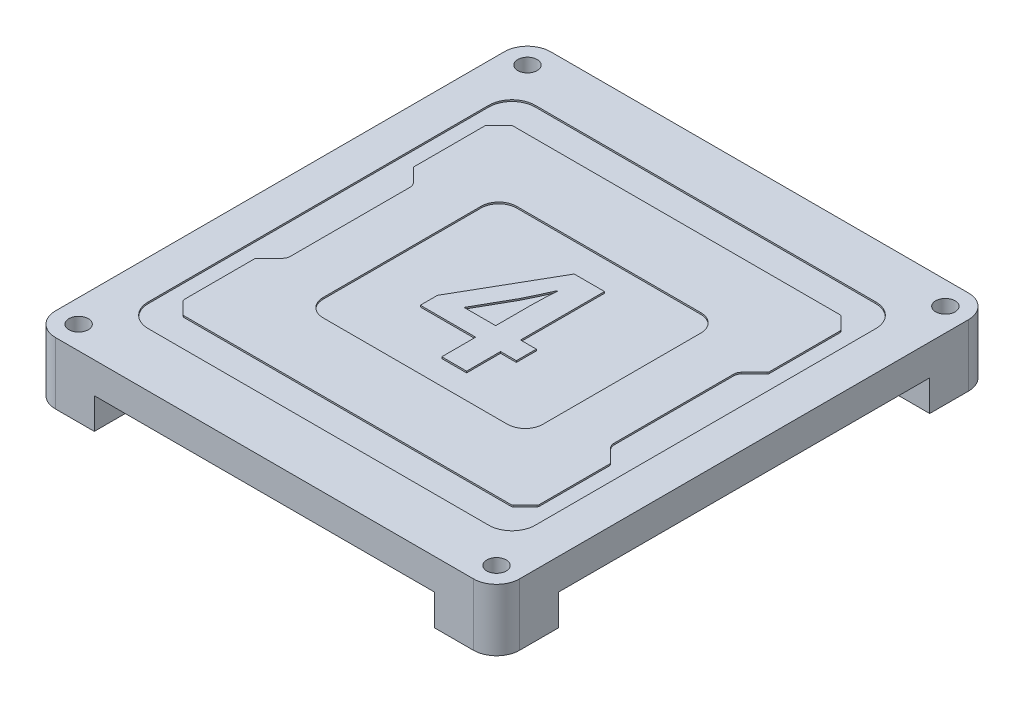
SolidWorks part; units mm, degrees
ref_plane "前视基准面" through (0, 0, 0) normal (0, 0, 1) x (1, 0, 0)
ref_plane "上视基准面" through (0, 0, 0) normal (0, 1, 0) x (1, 0, 0)
ref_plane "右视基准面" through (0, 0, 0) normal (1, 0, 0) x (0, 0, -1)
other "Configuration Table"
sketch "草图1" plane through (0, 0, 0) normal (0, 1, 0) x (1, 0, 0)
  line L8 (-27.0001, -31.9874) -> (27.0001, -31.9874)
  line L9 (29.9874, -29.0001) -> (29.9874, 29.0001)
  line L10 (27.0001, 31.9874) -> (-27.0001, 31.9874)
  line L11 (-29.9874, 29.0001) -> (-29.9874, -29.0001)
  line L12 (-27.0001, -31.9874) -> (27.0001, -31.9874)
  line L13 (29.9874, -29.0001) -> (29.9874, 29.0001)
  line L14 (27.0001, 31.9874) -> (-27.0001, 31.9874)
  line L15 (-29.9874, 29.0001) -> (-29.9874, -29.0001)
  arc A4 (27.0001, -31.9874) -> (29.9874, -29.0001) centre (27.0001, -29.0001) ccw
  arc A5 (29.9874, 29.0001) -> (27.0001, 31.9874) centre (27.0001, 29.0001) ccw
  arc A6 (-27.0001, 31.9874) -> (-29.9874, 29.0001) centre (-27.0001, 29.0001) ccw
  arc A7 (-29.9874, -29.0001) -> (-27.0001, -31.9874) centre (-27.0001, -29.0001) ccw
  arc A8 (27.0001, -31.9874) -> (29.9874, -29.0001) centre (27.0001, -29.0001) ccw
  arc A9 (29.9874, 29.0001) -> (27.0001, 31.9874) centre (27.0001, 29.0001) ccw
  arc A10 (-27.0001, 31.9874) -> (-29.9874, 29.0001) centre (-27.0001, 29.0001) ccw
  arc A11 (-29.9874, -29.0001) -> (-27.0001, -31.9874) centre (-27.0001, -29.0001) ccw
  dimension "D1" = 0
extrude "凸台-拉伸1" add sketch "草图1" along normal blind 4
sketch "草图2" plane through (0, 0, 0) normal (0, -1, 0) x (1, 0, 0)
  line L4 (-21.9874, 23.9874) -> (-21.9874, 31.9874)
  line L5 (-21.9874, 31.9874) -> (-27.0001, 31.9874)
  line L6 (-29.9874, 29.0001) -> (-29.9874, 23.9874)
  line L7 (-29.9874, 23.9874) -> (-21.9874, 23.9874)
  line L8 (-21.9874, 23.9874) -> (-21.9874, 31.9874)
  line L9 (-21.9874, 31.9874) -> (-27.0001, 31.9874)
  line L10 (-29.9874, 29.0001) -> (-29.9874, 23.9874)
  line L11 (-29.9874, 23.9874) -> (-21.9874, 23.9874)
  line L12 (21.9874, -23.9874) -> (21.9874, -31.9874)
  line L13 (21.9874, -31.9874) -> (27.0001, -31.9874)
  line L14 (29.9874, -29.0001) -> (29.9874, -23.9874)
  line L15 (29.9874, -23.9874) -> (21.9874, -23.9874)
  line L16 (21.9874, -23.9874) -> (21.9874, -31.9874)
  line L17 (21.9874, -31.9874) -> (27.0001, -31.9874)
  line L18 (29.9874, -29.0001) -> (29.9874, -23.9874)
  line L19 (29.9874, -23.9874) -> (21.9874, -23.9874)
  line L20 (21.9874, 23.9874) -> (29.9874, 23.9874)
  line L21 (29.9874, 23.9874) -> (29.9874, 29.0001)
  line L22 (27.0001, 31.9874) -> (21.9874, 31.9874)
  line L23 (21.9874, 31.9874) -> (21.9874, 23.9874)
  line L24 (21.9874, 23.9874) -> (29.9874, 23.9874)
  line L25 (29.9874, 23.9874) -> (29.9874, 29.0001)
  line L26 (27.0001, 31.9874) -> (21.9874, 31.9874)
  line L27 (21.9874, 31.9874) -> (21.9874, 23.9874)
  line L28 (-29.9874, -23.9874) -> (-29.9874, -29.0001)
  line L29 (-21.9874, -23.9874) -> (-29.9874, -23.9874)
  line L30 (-21.9874, -31.9874) -> (-21.9874, -23.9874)
  line L31 (-27.0001, -31.9874) -> (-21.9874, -31.9874)
  line L32 (-29.9874, -23.9874) -> (-29.9874, -29.0001)
  line L33 (-21.9874, -23.9874) -> (-29.9874, -23.9874)
  line L34 (-21.9874, -31.9874) -> (-21.9874, -23.9874)
  line L35 (-27.0001, -31.9874) -> (-21.9874, -31.9874)
  arc A1 (-27.0001, 31.9874) -> (-29.9874, 29.0001) centre (-27.0001, 29.0001) ccw
  arc A2 (-27.0001, 31.9874) -> (-29.9874, 29.0001) centre (-27.0001, 29.0001) ccw
  arc A3 (27.0001, -31.9874) -> (29.9874, -29.0001) centre (27.0001, -29.0001) ccw
  arc A4 (27.0001, -31.9874) -> (29.9874, -29.0001) centre (27.0001, -29.0001) ccw
  arc A5 (29.9874, 29.0001) -> (27.0001, 31.9874) centre (27.0001, 29.0001) ccw
  arc A6 (29.9874, 29.0001) -> (27.0001, 31.9874) centre (27.0001, 29.0001) ccw
  arc A7 (-29.9874, -29.0001) -> (-27.0001, -31.9874) centre (-27.0001, -29.0001) ccw
  arc A8 (-29.9874, -29.0001) -> (-27.0001, -31.9874) centre (-27.0001, -29.0001) ccw
  dimension "D1" = 0
  dimension "D2" = 0
  dimension "D3" = 0
  dimension "D4" = 0
extrude "凸台-拉伸2" add sketch "草图2" along normal blind 4
sketch "草图3" plane through (0, -4, 0) normal (0, -1, 0) x (1, 0, 0)
  circle A0 centre (-27.0001, 29.0001) radius 1.25
  circle A1 centre (27.0001, 29.0001) radius 1.25
  circle A2 centre (27.0001, -29.0001) radius 1.25
  circle A3 centre (-27.0001, -29.0001) radius 1.25
  dimension "D1" = 2.5
  dimension "D2" = 2.5
  dimension "D3" = 2.5
  dimension "D4" = 2.5
extrude "切除-拉伸1" cut sketch "草图3" against normal blind 15
sketch "草图4" plane through (0, 4, 0) normal (0, 1, 0) x (1, 0, 0)
  line L1 (-22, -25) -> (22, -25)
  line L2 (-25, -22) -> (-25, 22)
  line L3 (-22, 25) -> (22, 25)
  line L4 (25, -22) -> (25, 22)
  line L5 (0, 25) -> (0, -25) construction
  line L6 (-25, 0) -> (25, 0) construction
  arc A0 (-22, -25) -> (-25, -22) centre (-22, -22) cw
  arc A1 (25, 22) -> (22, 25) centre (22, 22) ccw
  arc A2 (25, -22) -> (22, -25) centre (22, -22) cw
  arc A3 (-25, 22) -> (-22, 25) centre (-22, 22) cw
  point P0 (0, 0)
  point P6 (-25, -25)
  point P16 (-25, 25)
  dimension "D2" = 3
  dimension "D1" = 50
extrude "切除-拉伸2" cut sketch "草图4" against normal blind 0.2
sketch "草图9" plane through (0, 3.8, 0) normal (0, 1, 0) x (1, 0, 0)
  line L4 (-20.91, 7.7375) -> (-20.91, -7.7375)
  line L5 (-21.2088, -8.4588) -> (-22.8504, -10.1004)
  line L6 (-22.95, -10.3408) -> (-22.95, -19.4092)
  line L7 (-22.8504, -19.6496) -> (-21.3496, -21.1504)
  line L8 (-21.1092, -21.25) -> (21.1092, -21.25)
  line L9 (21.3496, -21.1504) -> (22.8504, -19.6496)
  line L10 (22.95, -19.4092) -> (22.95, -10.3408)
  line L11 (22.8504, -10.1004) -> (21.2088, -8.4588)
  line L12 (20.91, -7.7375) -> (20.91, 7.7375)
  line L13 (21.2088, 8.4588) -> (22.8504, 10.1004)
  line L14 (22.95, 10.3408) -> (22.95, 19.4092)
  line L15 (22.8504, 19.6496) -> (21.3496, 21.1504)
  line L16 (21.1092, 21.25) -> (-21.1092, 21.25)
  line L17 (-21.3496, 21.1504) -> (-22.8504, 19.6496)
  line L18 (-22.95, 19.4092) -> (-22.95, 10.3408)
  line L19 (-22.8504, 10.1004) -> (-21.2088, 8.4588)
  line L20 (-11.9, -12.495) -> (11.9, -12.495)
  line L21 (14.195, -10.2) -> (14.195, 10.2)
  line L22 (-14.195, 10.2) -> (-14.195, -10.2)
  line L23 (11.9, 12.495) -> (-11.9, 12.495)
  line L24 (-11.9, 0) -> (11.9, 0) construction
  line L25 (0, 11.305) -> (0, -11.305) construction
  line L27 (-10.9, -10.2) -> (10.9, -10.2)
  line L28 (-11.9, -9.2) -> (-11.9, 9.2)
  line L29 (-10.9, 10.2) -> (10.9, 10.2)
  line L30 (11.9, -9.2) -> (11.9, 9.2)
  line L31 (0, 10.2) -> (0, -10.2) construction
  line L32 (-11.9, 0) -> (11.9, 0) construction
  arc A4 (-20.91, 7.7375) -> (-21.2088, 8.4588) centre (-21.93, 7.7375) ccw
  arc A5 (-21.2088, -8.4588) -> (-20.91, -7.7375) centre (-21.93, -7.7375) ccw
  arc A6 (-22.8504, -10.1004) -> (-22.95, -10.3408) centre (-22.61, -10.3408) ccw
  arc A7 (-22.95, -19.4092) -> (-22.8504, -19.6496) centre (-22.61, -19.4092) ccw
  arc A8 (-21.3496, -21.1504) -> (-21.1092, -21.25) centre (-21.1092, -20.91) ccw
  arc A9 (21.1092, -21.25) -> (21.3496, -21.1504) centre (21.1092, -20.91) ccw
  arc A10 (22.8504, -19.6496) -> (22.95, -19.4092) centre (22.61, -19.4092) ccw
  arc A11 (22.95, -10.3408) -> (22.8504, -10.1004) centre (22.61, -10.3408) ccw
  arc A12 (20.91, -7.7375) -> (21.2088, -8.4588) centre (21.93, -7.7375) ccw
  arc A13 (21.2088, 8.4588) -> (20.91, 7.7375) centre (21.93, 7.7375) ccw
  arc A14 (22.8504, 10.1004) -> (22.95, 10.3408) centre (22.61, 10.3408) ccw
  arc A15 (22.95, 19.4092) -> (22.8504, 19.6496) centre (22.61, 19.4092) ccw
  arc A16 (21.3496, 21.1504) -> (21.1092, 21.25) centre (21.1092, 20.91) ccw
  arc A17 (-21.1092, 21.25) -> (-21.3496, 21.1504) centre (-21.1092, 20.91) ccw
  arc A18 (-22.8504, 19.6496) -> (-22.95, 19.4092) centre (-22.61, 19.4092) ccw
  arc A19 (-22.95, 10.3408) -> (-22.8504, 10.1004) centre (-22.61, 10.3408) ccw
  arc A20 (-17.612, -17.765) -> (-14.688, -17.765) centre (-16.15, -17.765) ccw
  arc A21 (-14.688, -17.765) -> (-17.612, -17.765) centre (-16.15, -17.765) ccw
  arc A22 (14.688, 17.765) -> (17.612, 17.765) centre (16.15, 17.765) ccw
  arc A23 (17.612, 17.765) -> (14.688, 17.765) centre (16.15, 17.765) ccw
  arc A24 (-17.612, 17.765) -> (-14.688, 17.765) centre (-16.15, 17.765) ccw
  arc A25 (-14.688, 17.765) -> (-17.612, 17.765) centre (-16.15, 17.765) ccw
  arc A26 (17.612, -17.765) -> (14.688, -17.765) centre (16.15, -17.765) ccw
  arc A27 (14.688, -17.765) -> (17.612, -17.765) centre (16.15, -17.765) ccw
  arc A28 (-14.195, -10.2) -> (-11.9, -12.495) centre (-11.9, -10.2) ccw
  arc A29 (11.9, -12.495) -> (14.195, -10.2) centre (11.9, -10.2) ccw
  arc A30 (14.195, 10.2) -> (11.9, 12.495) centre (11.9, 10.2) ccw
  arc A31 (-11.9, 12.495) -> (-14.195, 10.2) centre (-11.9, 10.2) ccw
  arc A32 (-11.9, 9.2) -> (-10.9, 10.2) centre (-10.9, 9.2) cw
  arc A33 (11.9, -9.2) -> (10.9, -10.2) centre (10.9, -9.2) cw
  arc A34 (-10.9, -10.2) -> (-11.9, -9.2) centre (-10.9, -9.2) cw
  arc A35 (11.9, 9.2) -> (10.9, 10.2) centre (10.9, 9.2) ccw
  point P84 (0, 0)
  dimension "D1" = 1
extrude "凸台-拉伸5" add sketch "草图9" along normal blind 0.2 contours L18 A19 L19 A4 L4 A5 L5 A6 L6 A7 L7 A8 L8 A9 L9 A10 L10 A11 L11 A12 L12 A13 L13 A14 L14 A15 L15 A16 L16 A17 L17 A18 A31 L23 A30 L21 A29 L20 A28 L22 A27 A26 A25 A24 A23 A22
sketch "草图12" plane through (0, 3.8, 0) normal (0, 1, 0) x (1, 0, 0)
  text T0 "4" font "@Adobe Gothic Std B" height 18
extrude "凸台-拉伸6" add sketch "草图12" along normal blind 0.2
sketch "草图13" plane through (0, 3.8, 0) normal (0, 1, 0) x (1, 0, 0)
  circle A0 centre (-16.15, 17.765) radius 2.2806
  circle A1 centre (16.15, 17.765) radius 2.9348
  circle A2 centre (16.15, -17.765) radius 2.6308
  circle A3 centre (-16.15, -17.765) radius 2.8482
extrude "凸台-拉伸7" add sketch "草图13" along normal blind 0.2
sketch "草图16" plane through (0, 4, 0) normal (0, 1, 0) x (1, 0, 0)
  circle A0 centre (-17.6985, 17.3288) radius 1.5
  circle A1 centre (-17.6985, -16.5385) radius 1.5
  circle A2 centre (18.1136, -16.5385) radius 1.5
  dimension "D1" = 3
  dimension "D2" = 3
  dimension "D3" = 3
extrude "切除-拉伸8" [suppressed] cut sketch "草图16" against normal blind 0.2
